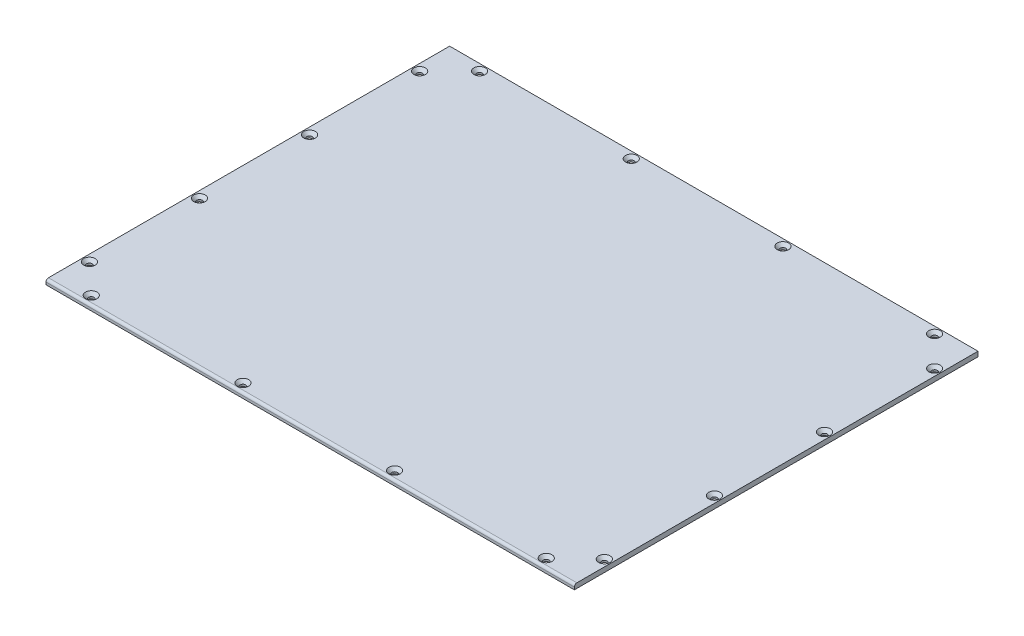
SolidWorks part; units mm, degrees
material "3.3523 (EN-AW 5052)"
ref_plane "前基準面" through (0, 0, 0) normal (0, 0, 1) x (1, 0, 0)
ref_plane "上基準面" through (0, 0, 0) normal (0, 1, 0) x (1, 0, 0)
ref_plane "右基準面" through (0, 0, 0) normal (1, 0, 0) x (0, 0, -1)
sketch "草圖2" plane through (0, 0, 0) normal (0, 1, 0) x (1, 0, 0)
  line L1 (0, 0) -> (432, 0)
  line L2 (0, 0) -> (0, 330)
  line L3 (0, 330) -> (432, 330)
  line L4 (432, 0) -> (432, 330)
  dimension "D1" = 330
  dimension "D2" = 432
extrude "填料-伸長1" add sketch "草圖2" along normal blind 4
fillet "圓角1" radius 2 1 edges at (216, 4, 0)
hole_wizard "M4 測板連接" positions "草圖3" profile "草圖4" countersink size "M4" standard "ISO" end condition through all
sketch "草圖3" plane through (0, 4, 0) normal (0, 1, 0) x (1, 0, 0)
  line L0 (432, 330) -> (0, 330) construction
  line L1 (0, 330) -> (0, 2) construction
  line L2 (0, 0) -> (432, 0) construction
  line L3 (432, 2) -> (432, 330) construction
  point P0 (30, 324.5)
  point P2 (154, 324.5)
  point P4 (278, 324.5)
  point P6 (402, 324.5)
  point P8 (426.5, 300)
  point P10 (426.5, 210)
  point P12 (426.5, 120)
  point P14 (426.5, 30)
  point P16 (402, 7)
  point P18 (278, 7)
  point P20 (154, 7)
  point P22 (30, 7)
  point P24 (5.5, 30)
  point P26 (5.5, 120)
  point P28 (5.5, 210)
  point P30 (5.5, 300)
  dimension "D1" = 5.5
  dimension "D2" = 5.5
  dimension "D3" = 30
  dimension "D4" = 124
  dimension "D5" = 124
  dimension "D6" = 124
  dimension "D7" = 30
  dimension "D8" = 90
  dimension "D9" = 90
  dimension "D10" = 90
  dimension "D11" = 7
  dimension "D12" = 5.5
sketch "草圖4" plane through (30, 4, -324.5) normal (1, 0, 0) x (0, 0, 1)
  line L0 (0, 0) -> (0, 4)
  line L1 (0, 4) -> (2.25, 4)
  line L2 (2.25, 4) -> (2.25, 2.45)
  line L3 (2.25, 2.45) -> (4.7, 0)
  line L5 (4.7, 0) -> (0, 0)
  line L6 (-2.25, 2.45) -> (-4.7, 0) construction
  line L11 (0, -6.35) -> (0, 107.95) construction
  dimension "貫穿孔直徑" = 4.5
  dimension "貫穿孔深度" = 4
  dimension "近端錐孔直徑" = 9.4
  dimension "近端錐孔角度" = 90
